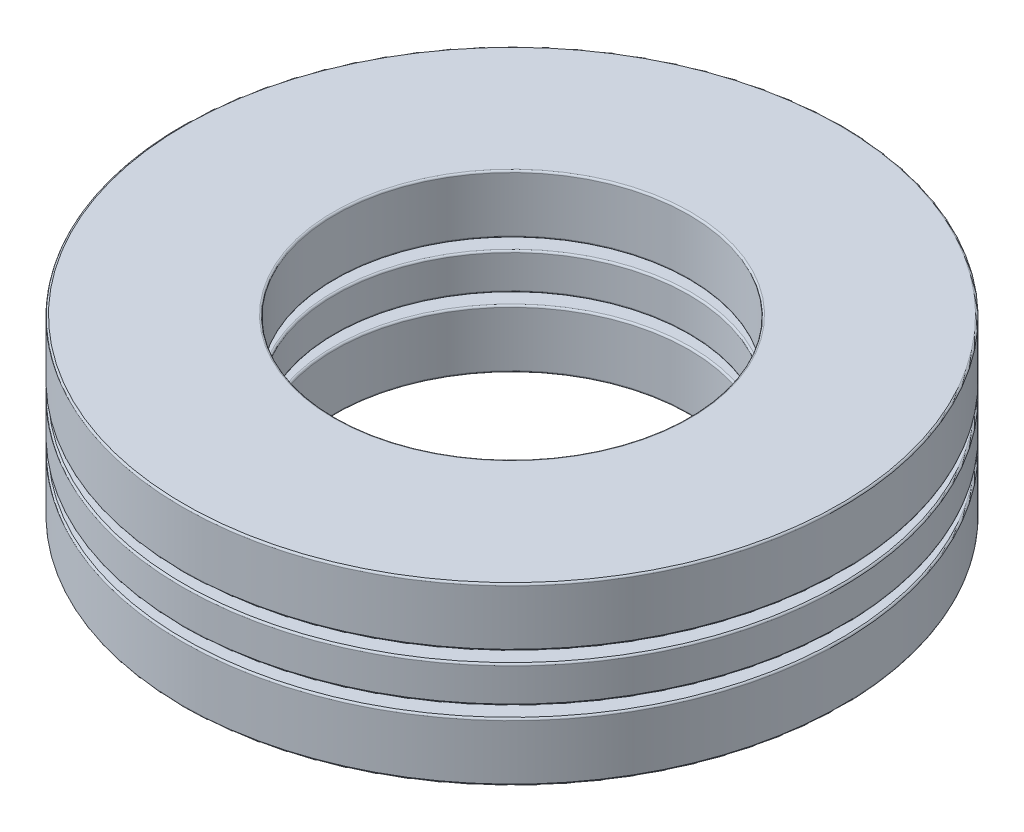
SolidWorks part; units mm, degrees
ref_plane "Front Plane" through (0, 0, 0) normal (0, 0, 1) x (1, 0, 0)
ref_plane "Top Plane" through (0, 0, 0) normal (0, 1, 0) x (1, 0, 0)
ref_plane "Right Plane" through (0, 0, 0) normal (1, 0, 0) x (0, 0, -1)
sketch "Sketch1" plane through (0, 0, 0) normal (1, 0, 0) x (0, 0, -1)
  line L0 (-11.9062, 0) -> (11.9062, 0) construction
  line L1 (0, -3.1623) -> (0, 3.1623) construction
  line L2 (-11.9062, 0.6588) -> (-6.3881, 0.6588)
  line L3 (-11.9062, 0.6588) -> (-11.9062, -0.6588)
  line L4 (-11.9062, -0.6588) -> (-6.3881, -0.6588)
  line L5 (-6.3881, 0.6588) -> (-6.3881, -0.6588)
  line L6 (-9.1472, 1.0541) -> (-9.1472, -1.0541) construction
  circle A0 centre (-9.1472, 0) radius 1.0541 construction
  point P13 (-9.1472, 0.6588)
  dimension "OD" = 23.8125
  dimension "Shaft Dia" = 12.7762
  dimension "Th" = 6.3246
  dimension "D1" = 2.1082
  dimension "D2" = 1.3176
revolve "Revolve1" add sketch "Sketch1" angle 360 about L1
sketch "Sketch3" plane through (0, 0, 0) normal (1, 0, 0) x (0, 0, -1)
  line L0 (-9.1472, 1.0541) -> (-9.1472, -1.0541)
  arc A0 (-9.1472, 1.0541) -> (-9.1472, -1.0541) centre (-9.1472, 0) ccw
  circle A1 centre (-9.1472, 0) radius 1.0541 construction
revolve "Cut-Revolve1" cut sketch "Sketch3" angle 360 about L0
sketch "Sketch2" plane through (0, 0, 0) normal (1, 0, 0) x (0, 0, -1)
  line L0 (-9.1472, 1.0541) -> (-9.1472, -1.0541)
  arc A0 (-9.1472, 1.0541) -> (-9.1472, -1.0541) centre (-9.1472, 0) ccw
  circle A2 centre (-9.1472, 0) radius 1.0541 construction
revolve "Revolve2" add sketch "Sketch2" angle 360 about L0
ref_axis "Axis1" through (0, 3.1623, 0) along (0, -1, 0)
pattern_circular "CirPattern1" count 5 every 72 about axis through (0, 3.1623, 0) along (0, -1, 0) of bodies 187
pattern_circular "CirPattern2" count 5 every 72 about axis through (0, 0, 0) along (0, 1, 0) of "Cut-Revolve1"
sketch "Sketch4" plane through (0, 0, 0) normal (1, 0, 0) x (0, 0, -1)
  line L0 (-11.9062, 0.6588) -> (-11.9062, -0.6588) construction
  line L1 (-11.9062, 1.0541) -> (-6.3881, 1.0541)
  line L2 (-11.9062, 1.0541) -> (-11.9062, 3.1623)
  line L3 (-11.9062, 3.1623) -> (-6.3881, 3.1623)
  line L4 (-6.3881, 1.0541) -> (-6.3881, 3.1623)
  line L5 (-11.9062, -3.1623) -> (-6.3881, -3.1623)
  line L6 (-11.9062, -3.1623) -> (-11.9062, -1.0541)
  line L7 (-11.9062, -1.0541) -> (-6.3881, -1.0541)
  line L8 (-6.3881, -3.1623) -> (-6.3881, -1.0541)
  line L9 (-9.1472, 1.0541) -> (-9.1472, -1.0541) construction
  line L10 (-6.3881, 0.6588) -> (-6.3881, -0.6588) construction
  line L11 (0, 0) -> (-11.9062, 0) construction
  line L12 (-11.9062, 0) -> (11.9062, 0) construction
  dimension "Ht" = 6.3246
revolve "Revolve3" add sketch "Sketch4" angle 360 about L1
fillet "Fillet1" radius 0.0632 4 edges at (0, 1.0541, -6.3881) (0, 3.1623, -6.3881) (0, 1.0541, -11.9062) (0, 3.1623, -11.9062)
fillet "Fillet2" radius 0.0632 4 edges at (0, -0.6588, -6.3881) (0, 0.6588, -6.3881) (0, -0.6588, -11.9062) (0, 0.6588, -11.9062)
fillet "Fillet3" radius 0.0632 4 edges at (0, -3.1623, -6.3881) (0, -1.0541, -6.3881) (0, -3.1623, -11.9062) (0, -1.0541, -11.9062)
equation "\"D1@Sketch1\" = \"Th@Sketch1\"/3"
equation "\"D2@Sketch1\" = \"D1@Sketch1\"*.625"
equation "\"Balls@CirPattern1\" = \"OD@Sketch1\"*5"
equation "\"Angle@CirPattern1\" = 360/\"Balls@CirPattern1\""
equation "\"D1@CirPattern2\" = \"Balls@CirPattern1\""
equation "\"D2@CirPattern2\" = \"Angle@CirPattern1\""
equation "\"D1@Fillet1\" = \"Th@Sketch1\"*.01"
equation "\"D1@Fillet2\" = \"D1@Fillet1\""
equation "\"D1@Fillet3\" = \"D1@Fillet1\""
